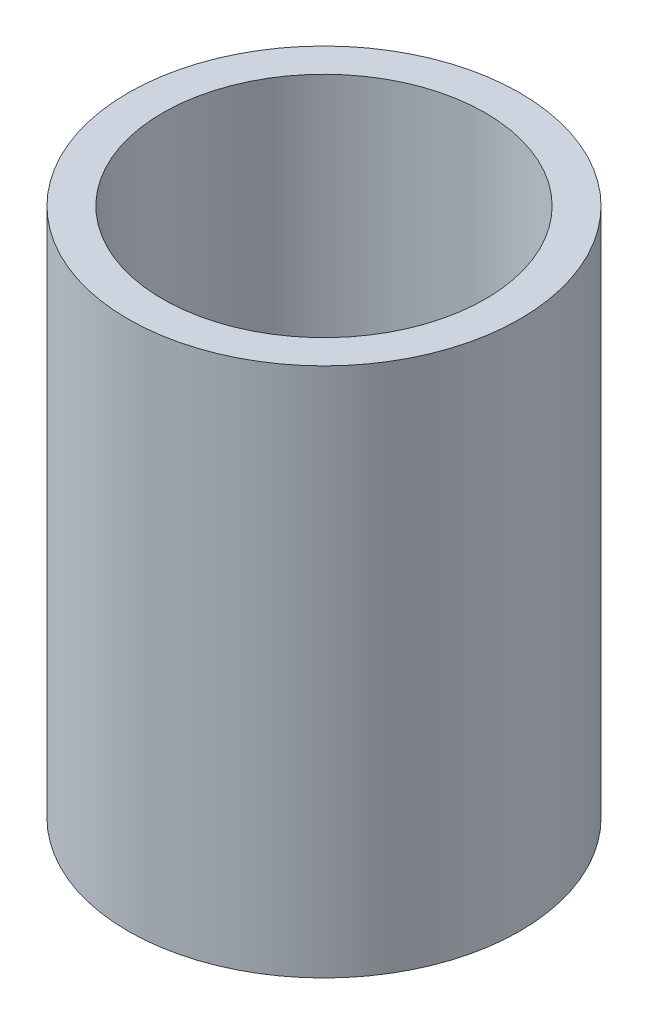
SolidWorks part; units mm, degrees
ref_plane "Płaszczyzna przednia" through (0, 0, 0) normal (0, 0, 1) x (1, 0, 0)
ref_plane "Płaszczyzna górna" through (0, 0, 0) normal (0, 1, 0) x (1, 0, 0)
ref_plane "Płaszczyzna prawa" through (0, 0, 0) normal (1, 0, 0) x (0, 0, -1)
sketch "Szkic1" plane through (0, 0, 0) normal (0, 0, 1) x (1, 0, 0)
  line L0 (0, 0) -> (0, 22.9271) construction
  line L1 (8.5, 0) -> (8.5, 23)
  line L2 (7, 0) -> (7, 4)
  line L3 (7, 4) -> (0, 4)
  line L4 (7, 0) -> (8.5, 0)
  line L5 (8.5, 23) -> (7, 23)
  line L6 (7, 23) -> (7, 12)
  line L7 (7, 12) -> (5.1962, 12)
  line L8 (0, 4) -> (0, 9)
  line L9 (0, 9) -> (5.1962, 12)
  dimension "D1" = 23
  dimension "D2" = 11
  dimension "D3" = 14
  dimension "D4" = 60
  dimension "D5" = 4
  dimension "D6" = 7
  dimension "D7" = 1.5
revolve "Obrót2" add sketch "Szkic1" angle 360 about L0
